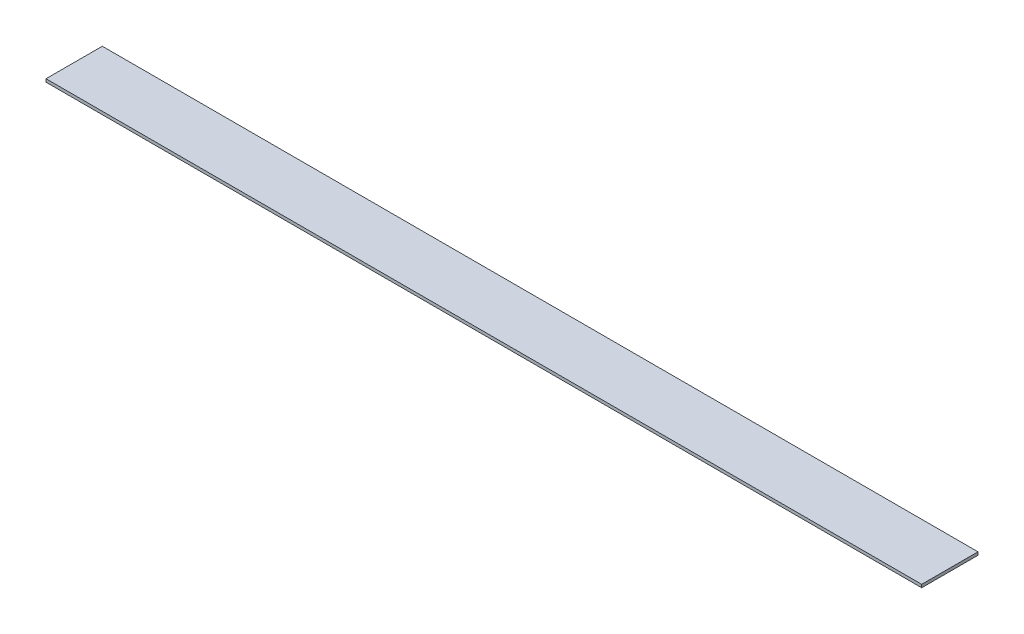
SolidWorks part; units mm, degrees
material "Acrylic (Medium-high impact)"
ref_plane "Front Plane" through (0, 0, 0) normal (0, 0, 1) x (1, 0, 0)
ref_plane "Top Plane" through (0, 0, 0) normal (0, 1, 0) x (1, 0, 0)
ref_plane "Right Plane" through (0, 0, 0) normal (1, 0, 0) x (0, 0, -1)
sketch "Sketch1" plane through (0, 0, 0) normal (0, 1, 0) x (1, 0, 0)
  line L1 (0, 0) -> (923.925, 0)
  line L2 (0, 0) -> (0, 59.4)
  line L3 (0, 59.4) -> (923.925, 59.4)
  line L4 (923.925, 0) -> (923.925, 59.4)
  dimension "D1" = 923.925
  dimension "D2" = 59.4
extrude "Boss-Extrude1" add sketch "Sketch1" along normal blind 3.175 contours L2 L3 L4 L1
